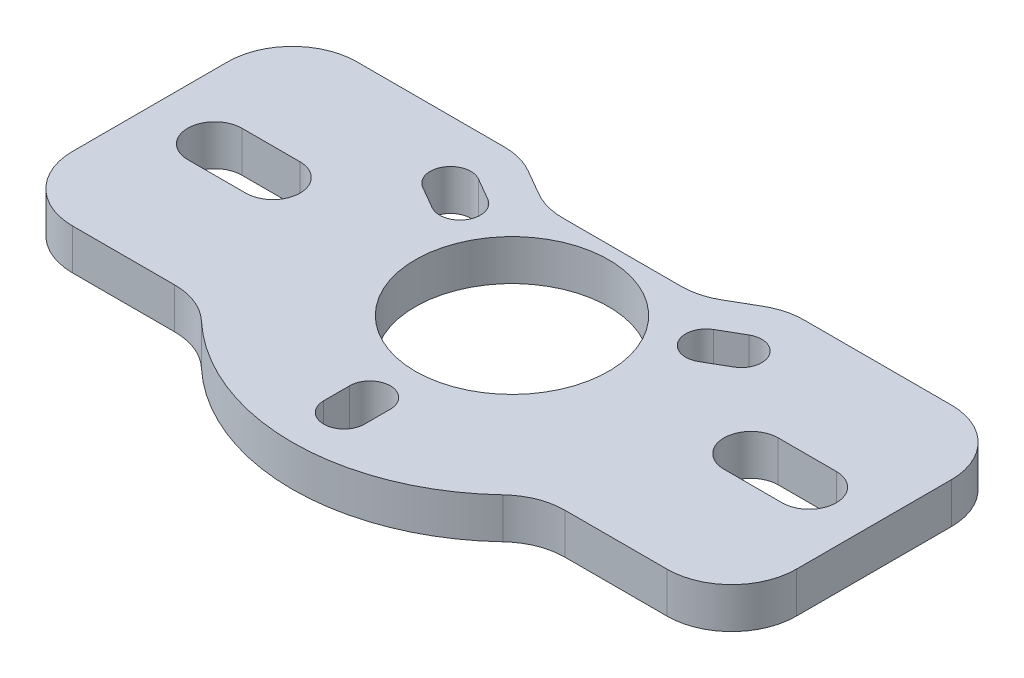
SolidWorks part; units mm, degrees
material "CA"
ref_plane "Front Plane" through (0, 0, 0) normal (0, 0, 1) x (1, 0, 0)
ref_plane "Top Plane" through (0, 0, 0) normal (0, 1, 0) x (1, 0, 0)
ref_plane "Right Plane" through (0, 0, 0) normal (1, 0, 0) x (0, 0, -1)
sketch "Sketch1" plane through (0, 0, 0) normal (0, 1, 0) x (1, 0, 0)
  line L0 (14.7222, 13.97) -> (29.21, 13.97)
  line L1 (-29.21, 13.97) -> (-14.7222, 13.97)
  line L2 (-35.56, 7.62) -> (-35.56, -7.62)
  line L3 (-11.5472, 13.1193) -> (-8.995, 11.6457)
  line L4 (35.56, 7.62) -> (35.56, -7.62)
  line L5 (-23.495, 0) -> (-29.21, 0) construction
  line L6 (-23.495, -2.667) -> (-29.21, -2.667)
  line L7 (-23.495, 2.667) -> (-29.21, 2.667)
  line L8 (23.495, 0) -> (29.21, 0) construction
  line L9 (23.495, 2.667) -> (29.21, 2.667)
  line L10 (23.495, -2.667) -> (29.21, -2.667)
  line L11 (-14.2894, 8.25) -> (0, 0) construction
  line L12 (0, 0) -> (14.2894, 8.25) construction
  line L13 (-15.2894, 6.5179) -> (-13.0897, 5.2479)
  line L14 (-13.2894, 9.9821) -> (-11.0897, 8.7121)
  line L15 (13.2894, 9.9821) -> (11.0897, 8.7121)
  line L16 (15.2894, 6.5179) -> (13.0897, 5.2479)
  line L17 (2, -16.5) -> (2, -13.96)
  line L18 (-2, -13.96) -> (-2, -16.5)
  line L19 (-29.21, -13.97) -> (-19.1766, -13.97)
  line L20 (19.1766, -13.97) -> (29.21, -13.97)
  line L21 (-5.82, 10.795) -> (5.82, 10.795)
  line L22 (8.995, 11.6457) -> (11.5472, 13.1193)
  circle A0 centre (0, 0) radius 5.75
  arc A1 (-23.495, -2.667) -> (-23.495, 2.667) centre (-23.495, 0) ccw
  arc A2 (-29.21, 2.667) -> (-29.21, -2.667) centre (-29.21, 0) ccw
  arc A3 (23.495, 2.667) -> (23.495, -2.667) centre (23.495, 0) ccw
  arc A4 (29.21, -2.667) -> (29.21, 2.667) centre (29.21, 0) ccw
  arc A5 (-13.2894, 9.9821) -> (-15.2894, 6.5179) centre (-14.2894, 8.25) ccw
  arc A6 (15.2894, 6.5179) -> (13.2894, 9.9821) centre (14.2894, 8.25) ccw
  circle A7 centre (0, 0) radius 20 construction
  arc A8 (29.21, 13.97) -> (35.56, 7.62) centre (29.21, 7.62) cw
  arc A9 (29.21, -13.97) -> (35.56, -7.62) centre (29.21, -7.62) ccw
  arc A10 (19.1766, -13.97) -> (14.8183, -15.7018) centre (19.1766, -20.32) ccw
  arc A11 (-29.21, 13.97) -> (-35.56, 7.62) centre (-29.21, 7.62) ccw
  circle A12 centre (0, 0) radius 16.5 construction
  arc A13 (-2, -16.5) -> (2, -16.5) centre (0, -16.5) ccw
  arc A14 (5.82, 10.795) -> (8.995, 11.6457) centre (5.82, 17.145) ccw
  arc A15 (11.5472, 13.1193) -> (14.7222, 13.97) centre (14.7222, 7.62) cw
  arc A16 (-14.7222, 13.97) -> (-11.5472, 13.1193) centre (-14.7222, 7.62) cw
  arc A17 (-13.0897, 5.2479) -> (-11.0897, 8.7121) centre (-12.0897, 6.98) ccw
  arc A18 (11.0897, 8.7121) -> (13.0897, 5.2479) centre (12.0897, 6.98) ccw
  arc A19 (2, -13.96) -> (-2, -13.96) centre (0, -13.96) ccw
  arc A20 (-14.8183, -15.7018) -> (14.8183, -15.7018) centre (0, 0) ccw
  arc A21 (-19.1766, -13.97) -> (-14.8183, -15.7018) centre (-19.1766, -20.32) cw
  arc A22 (-29.21, -13.97) -> (-35.56, -7.62) centre (-29.21, -7.62) cw
  arc A23 (-8.995, 11.6457) -> (-5.82, 10.795) centre (-5.82, 17.145) ccw
  point P9 (-26.3525, 0)
  point P14 (26.3525, 0)
  point P42 (11.6397, 13.97)
  point P50 (-16.4611, -13.97)
  dimension "D3" = 11.5
  dimension "D10" = 40
  dimension "D11" = 6.35
  dimension "D8" = 33
  dimension "D9" = 4
  dimension "D13" = 10.795
  dimension "D18" = 6.35
  dimension "D16" = 21.59
  dimension "D21" = 6.35
  dimension "D14" = 6.35
  dimension "D2" = 71.12
  dimension "D4" = 23.495
  dimension "D5" = 23.495
  dimension "D6" = 29.21
  dimension "D7" = 5.334
  dimension "D12" = 120
  dimension "D15" = 13.97
  dimension "D17" = 35.56
  dimension "D19" = 2.54
  dimension "D20" = 13.97
  dimension "D22" = 5.588
  dimension "D23" = 5.588
extrude "Boss-Extrude1" add sketch "Sketch1" along normal blind 4
sketch "Sketch5" plane through (0, 4, 0) normal (0, 1, 0) x (1, 0, 0)
  line L0 (-3.9688, -13.96) -> (-3.9688, -16.5)
  line L1 (3.9688, -16.5) -> (3.9688, -13.96)
  line L2 (12.305, 11.687) -> (10.1053, 10.417)
  line L3 (16.2738, 4.813) -> (14.0741, 3.543)
  line L4 (-12.305, 11.687) -> (-10.1053, 10.417)
  line L5 (-16.2738, 4.813) -> (-14.0741, 3.543)
  arc A0 (16.2738, 4.813) -> (12.305, 11.687) centre (14.2894, 8.25) ccw
  arc A1 (-12.305, 11.687) -> (-16.2738, 4.813) centre (-14.2894, 8.25) ccw
  arc A2 (-3.9688, -16.5) -> (3.9688, -16.5) centre (0, -16.5) ccw
  arc A3 (-14.0741, 3.543) -> (-10.1053, 10.417) centre (-12.0897, 6.98) ccw
  arc A4 (3.9688, -13.96) -> (-3.9688, -13.96) centre (0, -13.96) ccw
  arc A5 (10.1053, 10.417) -> (14.0741, 3.543) centre (12.0897, 6.98) ccw
  dimension "D1" = 7.9375
ref_plane "Plane1" through (0, 0, 0) normal (0.5, 0, 0.866) x (0.866, 0, -0.5)
sketch "Sketch6" plane through (0, 4, 0) normal (0, 1, 0) x (1, 0, 0)
  circle A0 centre (0, 0) radius 9.5
  circle A1 centre (0, 0) radius 5.75 construction
  dimension "D1" = 3.75
extrude "Cut-Extrude1" cut sketch "Sketch6" against normal through all
